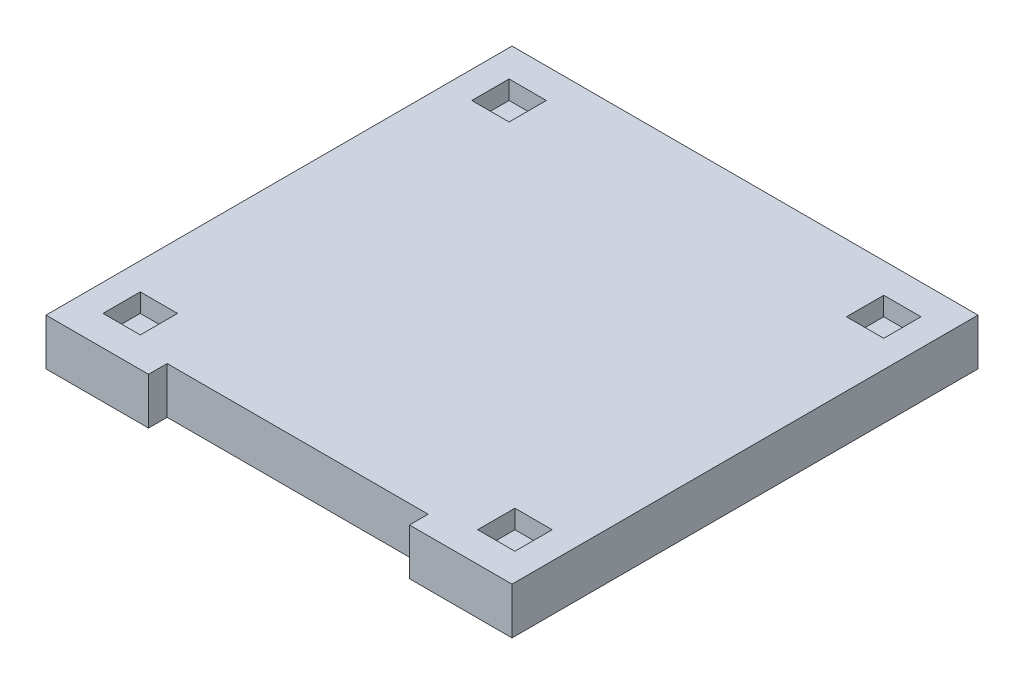
SolidWorks part; units mm, degrees
ref_plane "前视基准面" through (0, 0, 0) normal (0, 0, 1) x (1, 0, 0)
ref_plane "上视基准面" through (0, 0, 0) normal (0, 1, 0) x (1, 0, 0)
ref_plane "右视基准面" through (0, 0, 0) normal (1, 0, 0) x (0, 0, -1)
sketch "草图1" plane through (-338.1844, 0, 1455.4074) normal (0, 1, 0) x (1, 0, 0)
  line L0 (-911.8156, 1455.4074) -> (1588.1844, 1455.4074) construction
  line L1 (-911.8156, 2705.4074) -> (1588.1844, 2705.4074)
  line L2 (-911.8156, 2705.4074) -> (-911.8156, 205.4074)
  line L3 (-911.8156, 205.4074) -> (1588.1844, 205.4074)
  line L4 (1588.1844, 2705.4074) -> (1588.1844, 205.4074)
  line L5 (338.1844, 2705.4074) -> (338.1844, 205.4074) construction
  point P4 (338.1844, 2705.4074)
  point P5 (-911.8156, 1455.4074)
  point P6 (338.1844, 205.4074)
  point P7 (1588.1844, 1455.4074)
  point P12 (338.1844, 1455.4074)
extrude "凸台-拉伸2" add sketch "草图1" along normal blind 250 contours L4 L3 L2 L1
ref_plane "基准面2" through (0, 250, 0) normal (0, 1, 0) x (1, 0, 0)
sketch "草图5" plane through (0, 250, 0) normal (0, 1, 0) x (1, 0, 0)
  line L1 (1104.9828, -1089.3285) -> (904.9828, -1089.3285)
  line L2 (1104.9828, -1089.3285) -> (1104.9828, -889.3285)
  line L3 (1104.9828, -889.3285) -> (904.9828, -889.3285)
  line L4 (904.9828, -1089.3285) -> (904.9828, -889.3285)
  line L5 (1104.9828, -1089.3285) -> (904.9828, -889.3285) construction
  line L6 (1104.9828, -889.3285) -> (904.9828, -1089.3285) construction
  point P0 (1004.9828, -989.3285)
  point P2 (1004.9828, -989.3285)
extrude "切除-拉伸1" cut sketch "草图5" against normal blind 100 contours L3 L4 L1 L2
sketch "草图6" plane through (0, 250, 0) normal (0, 1, 0) x (1, 0, 0)
  line L0 (1250, 0) -> (-1250, 0) construction
  line L1 (1250, 1250) -> (1250, -1250) construction
  line L2 (-1250, 1250) -> (-1250, -1250) construction
  line L3 (0, 1250) -> (0, -1250) construction
  line L4 (-1250, 1250) -> (1250, 1250) construction
  line L5 (-1250, -1250) -> (1250, -1250) construction
  line L6 (904.9828, 1089.3285) -> (1104.9828, 1089.3285)
  line L7 (904.9828, 889.3285) -> (904.9828, 1089.3285)
  line L8 (1104.9828, 889.3285) -> (904.9828, 889.3285)
  line L9 (1104.9828, 1089.3285) -> (1104.9828, 889.3285)
  line L10 (1104.9828, -1089.3285) -> (1104.9828, -889.3285)
  line L11 (1104.9828, -889.3285) -> (904.9828, -889.3285)
  line L12 (904.9828, -889.3285) -> (904.9828, -1089.3285)
  line L13 (904.9828, -1089.3285) -> (1104.9828, -1089.3285)
  line L14 (1104.9828, -1089.3285) -> (1104.9828, -889.3285)
  line L15 (1104.9828, -889.3285) -> (904.9828, -889.3285)
  line L16 (904.9828, -889.3285) -> (904.9828, -1089.3285)
  line L17 (904.9828, -1089.3285) -> (1104.9828, -1089.3285)
  dimension "D1" = 0
extrude "切除-拉伸2" cut sketch "草图6" against normal blind 100 contours L6 L9 L8 L7
sketch "草图7" plane through (0, 250, 0) normal (0, 1, 0) x (1, 0, 0)
  line L0 (0, 1250) -> (0, -1250) construction
  line L1 (-1250, 1250) -> (1250, 1250) construction
  line L2 (-1250, -1250) -> (1250, -1250) construction
  line L3 (904.9828, 1089.3285) -> (904.9828, 889.3285) construction
  line L4 (904.9828, 889.3285) -> (1104.9828, 889.3285) construction
  line L5 (1104.9828, 889.3285) -> (1104.9828, 1089.3285) construction
  line L6 (1104.9828, 1089.3285) -> (904.9828, 1089.3285) construction
  line L7 (1104.9828, -1089.3285) -> (1104.9828, -889.3285) construction
  line L8 (1104.9828, -889.3285) -> (904.9828, -889.3285) construction
  line L9 (904.9828, -889.3285) -> (904.9828, -1089.3285) construction
  line L10 (904.9828, -1089.3285) -> (1104.9828, -1089.3285) construction
  line L11 (904.9828, 1089.3285) -> (904.9828, 889.3285)
  line L12 (904.9828, 889.3285) -> (1104.9828, 889.3285)
  line L13 (1104.9828, 889.3285) -> (1104.9828, 1089.3285)
  line L14 (1104.9828, 1089.3285) -> (904.9828, 1089.3285)
  line L15 (1104.9828, -1089.3285) -> (1104.9828, -889.3285)
  line L16 (1104.9828, -889.3285) -> (904.9828, -889.3285)
  line L17 (904.9828, -889.3285) -> (904.9828, -1089.3285)
  line L18 (904.9828, -1089.3285) -> (1104.9828, -1089.3285)
  line L19 (-904.9828, -1089.3285) -> (-1104.9828, -1089.3285)
  line L20 (-904.9828, -889.3285) -> (-904.9828, -1089.3285)
  line L21 (-1104.9828, -889.3285) -> (-904.9828, -889.3285)
  line L22 (-1104.9828, -1089.3285) -> (-1104.9828, -889.3285)
  line L23 (-1104.9828, 1089.3285) -> (-904.9828, 1089.3285)
  line L24 (-1104.9828, 889.3285) -> (-1104.9828, 1089.3285)
  line L25 (-904.9828, 889.3285) -> (-1104.9828, 889.3285)
  line L26 (-904.9828, 1089.3285) -> (-904.9828, 889.3285)
extrude "切除-拉伸3" cut sketch "草图7" against normal blind 100
sketch "草图9" plane through (0, 250, 0) normal (0, 1, 0) x (1, 0, 0)
  line L0 (-700, -1250) -> (700, -1250)
  line L1 (-1250, -1250) -> (1250, -1250) construction
  line L2 (-700, -1150) -> (0, -1150)
  line L3 (0, -1150) -> (700, -1150)
  line L4 (700, -1150) -> (700, -1250)
  line L5 (-700, -1150) -> (-700, -1250)
extrude "切除-拉伸4" cut sketch "草图9" against normal blind 250
